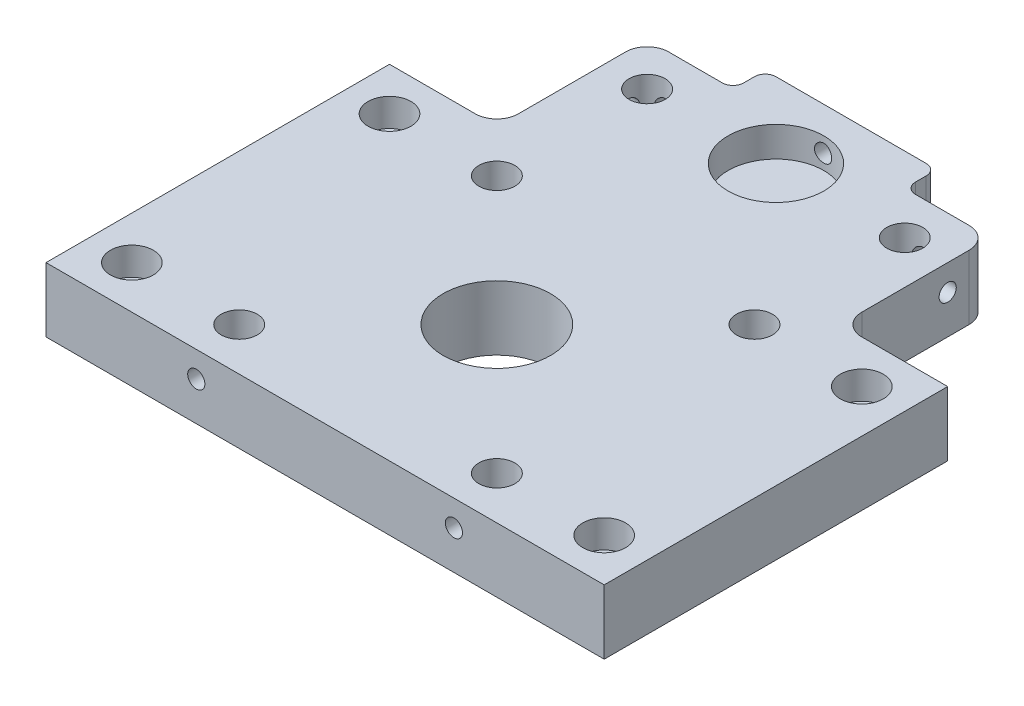
SolidWorks part; units mm, degrees
material "ABS"
ref_plane "Plano frontal" through (0, 0, 0) normal (0, 0, 1) x (1, 0, 0)
ref_plane "Plano superior" through (0, 0, 0) normal (0, 1, 0) x (1, 0, 0)
ref_plane "Plano direito" through (0, 0, 0) normal (1, 0, 0) x (0, 0, -1)
sketch "Esboço1" plane through (0, 0, 0) normal (0, 1, 0) x (1, 0, 0)
  line L1 (65, -65) -> (-65, -65)
  line L2 (65, -65) -> (65, 65)
  line L3 (65, 65) -> (-65, 65)
  line L4 (-65, -65) -> (-65, 65)
  line L5 (65, -65) -> (-65, 65) construction
  line L6 (65, 65) -> (-65, -65) construction
  point P0 (0, 0)
  dimension "D1" = 130
  dimension "D2" = 130
extrude "Ressalto-extrusão1" add sketch "Esboço1" along normal blind 15
sketch "Esboço2" plane through (0, 15, 0) normal (0, 1, 0) x (1, 0, 0)
  line L0 (0, -72.4873) -> (0, 76.1731) construction
  line L1 (-65, 15) -> (65, 15) construction
  line L2 (-65, 65) -> (-65, -65) construction
  line L3 (65, -65) -> (65, 65) construction
  line L4 (-65, -65) -> (65, -65) construction
  line L5 (-40, 65) -> (-40, -65) construction
  line L6 (65, 65) -> (-65, 65) construction
  line L7 (40, 65) -> (40, -65) construction
  line L8 (-65, -25) -> (65, -25) construction
  line L9 (-40, 40) -> (40, 40) construction
  circle A0 centre (-30, 5) radius 4.2
  circle A1 centre (30, 5) radius 4.2
  circle A2 centre (30, -55) radius 4.2
  circle A3 centre (-30, -55) radius 4.2
  circle A4 centre (-30, 40) radius 4.2
  circle A5 centre (30, 40) radius 4.2
  dimension "D5" = 8.4
  dimension "D7" = 10
  dimension "D1" = 80
  dimension "D2" = 40
  dimension "D3" = 40
  dimension "D4" = 40
  dimension "D6" = 10
  dimension "D8" = 25
  dimension "D9" = 10
extrude "Corte-extrusão1" cut sketch "Esboço2" against normal blind 12
sketch "Esboço3" plane through (0, 15, 0) normal (0, 1, 0) x (1, 0, 0)
  line L0 (0, -72.7603) -> (0, 80.4323) construction
  line L1 (-65, 15) -> (65, 15) construction
  line L2 (-65, 65) -> (-65, -65) construction
  line L3 (65, -65) -> (65, 65) construction
  line L4 (-65, -65) -> (65, -65) construction
  line L5 (-65, -25) -> (65, -25) construction
  circle A0 centre (0, -25) radius 12.5
  dimension "D3" = 25
  dimension "D1" = 80
  dimension "D2" = 40
extrude "Corte-extrusão2" cut sketch "Esboço3" against normal through all
sketch "Esboço4" plane through (0, 15, 0) normal (0, 1, 0) x (1, 0, 0)
  line L0 (-65, 15) -> (65, 15) construction
  line L1 (-65, 65) -> (-65, -65) construction
  line L2 (65, -65) -> (65, 65) construction
  line L3 (65, 65) -> (-65, 65) construction
  line L4 (0, 91.3368) -> (0, -92.976) construction
  line L5 (-65, 40) -> (65, 40) construction
  circle A0 centre (0, 40) radius 11.15
  dimension "D3" = 22.3
  dimension "D1" = 50
  dimension "D2" = 25
extrude "Corte-extrusão3" cut sketch "Esboço4" against normal blind 7
sketch "Esboço5" plane through (0, 15, 0) normal (0, 1, 0) x (1, 0, 0)
  line L0 (0, 76.468) -> (0, -74.8954) construction
  line L1 (-65, 65) -> (-40, 65)
  line L2 (-65, 65) -> (-65, 15)
  line L3 (-65, 15) -> (-40, 15)
  line L4 (-40, 65) -> (-40, 15)
  line L5 (40, 65) -> (40, 15)
  line L6 (65, 15) -> (40, 15)
  line L7 (65, 65) -> (65, 15)
  line L8 (65, 65) -> (40, 65)
  dimension "D1" = 50
  dimension "D2" = 25
extrude "Corte-extrusão4" cut sketch "Esboço5" against normal through all
fillet "Filete1" radius 5 2 edges at (40, 7.5, -65) (-40, 7.5, -65)
sketch "Esboço6" plane through (0, 15, 0) normal (0, 1, 0) x (1, 0, 0)
  line L0 (-74.262, -25) -> (70.9857, -25) construction
  line L1 (0, 74.1091) -> (0, -76.8611) construction
  line L2 (-65, 15) -> (-40, 15) construction
  line L3 (-65, 15) -> (-65, -65) construction
  circle A0 centre (-55, 5) radius 5
  circle A1 centre (55, 5) radius 5
  circle A2 centre (55, -55) radius 5
  circle A3 centre (-55, -55) radius 5
  dimension "D1" = 10
  dimension "D3" = 10
  dimension "D2" = 10
extrude "Corte-extrusão5" cut sketch "Esboço6" against normal blind 6.5
sketch "Esboço7" plane through (0, 8.5, 0) normal (0, 1, 0) x (1, 0, 0)
  line L0 (-65, -25) -> (65, -25) construction
  line L1 (-65, 15) -> (-65, -65) construction
  line L2 (65, -65) -> (65, 15) construction
  line L3 (0, 65) -> (0, -65) construction
  line L4 (35, 65) -> (-35, 65) construction
  line L5 (-65, -65) -> (65, -65) construction
  circle A0 centre (-55, 5) radius 3
  circle A1 centre (-55, 5) radius 5 construction
  circle A2 centre (55, 5) radius 3
  circle A3 centre (55, -55) radius 3
  circle A4 centre (-55, -55) radius 3
  dimension "D1" = 6
extrude "Corte-extrusão6" cut sketch "Esboço7" against normal through all
sketch "Esboço8" plane through (0, 15, 0) normal (0, 1, 0) x (1, 0, 0)
  line L0 (0, 95.8386) -> (0, -83.9991) construction
  line L1 (35, 65) -> (-35, 65) construction
  line L2 (7.5, 72.5) -> (-7.5, 72.5)
  line L3 (7.5, 72.5) -> (7.5, 57.5)
  line L4 (7.5, 57.5) -> (-7.5, 57.5)
  line L5 (-7.5, 72.5) -> (-7.5, 57.5)
  line L6 (7.5, 72.5) -> (-7.5, 57.5) construction
  line L7 (7.5, 57.5) -> (-7.5, 72.5) construction
  point P3 (0, 65)
  dimension "D1" = 15
  dimension "D2" = 15
extrude "Corte-extrusão7" cut sketch "Esboço8" against normal through all
sketch "Esboço9" plane through (0, 0, -57.5) normal (0, 0, -1) x (-1, 0, 0)
  line L0 (0, -8.9377) -> (0, 25.8913) construction
  line L1 (7.5, 15) -> (-7.5, 15) construction
  circle A0 centre (0, 11.5) radius 2
  dimension "D1" = 3.5
  dimension "D2" = 4
extrude "Corte-extrusão8" cut sketch "Esboço9" against normal blind 10
sketch "Esboço10" plane through (-40, 0, 0) normal (-1, 0, 0) x (0, 0, 1)
  line L0 (-15, 15) -> (-60, 15) construction
  line L1 (-65, 0) -> (-65, 15) construction
  circle A0 centre (-40, 9) radius 2
  dimension "D1" = 4
  dimension "D2" = 6
  dimension "D3" = 25
extrude "Corte-extrusão9" cut sketch "Esboço10" against normal blind 10
sketch "Esboço11" plane through (40, 0, 0) normal (1, 0, 0) x (0, 0, -1)
  line L0 (65, 15) -> (65, 0) construction
  line L1 (60, 15) -> (15, 15) construction
  circle A0 centre (40, 9) radius 2
  dimension "D1" = 4
  dimension "D2" = 25
  dimension "D3" = 6
extrude "Corte-extrusão10" cut sketch "Esboço11" against normal blind 10
sketch "Esboço12" plane through (0, 0, 65) normal (0, 0, 1) x (1, 0, 0)
  line L0 (-65, 15) -> (-65, 0) construction
  line L1 (-65, 15) -> (65, 15) construction
  line L2 (0, -19.0544) -> (0, 30.5861) construction
  circle A0 centre (-30, 9) radius 2
  circle A1 centre (30, 9) radius 2
  dimension "D1" = 35
  dimension "D2" = 4
  dimension "D3" = 6
extrude "Corte-extrusão11" cut sketch "Esboço12" against normal blind 10
fillet "Filete2" radius 5 2 edges at (-40, 7.5, -15) (40, 7.5, -15)
sketch "Esboço13" plane through (0, 15, 0) normal (0, 1, 0) x (1, 0, 0)
  line L5 (-7.5, 57.5) -> (-20, 57.5)
  line L6 (-40, 20) -> (-40, 60) construction
  line L8 (-30, 34.8368) -> (-30, 45.3155) construction
  line L9 (0, -77.4538) -> (0, 84.4836) construction
  line L14 (-7.5, 57.5) -> (-7.5, 65)
  line L15 (-7.5, 65) -> (-40, 65)
  line L16 (-40, 65) -> (-40, 57.5)
  line L17 (-40, 50) -> (-20, 50)
  line L18 (-20, 50) -> (-20, 57.5)
  line L19 (-40, 50) -> (-40, 57.5)
  line L20 (7.5, 57.5) -> (7.5, 65)
  line L21 (7.5, 65) -> (40, 65)
  line L22 (40, 65) -> (40, 57.5)
  line L23 (40, 50) -> (40, 57.5)
  line L24 (40, 50) -> (20, 50)
  line L25 (20, 50) -> (20, 57.5)
  line L26 (7.5, 57.5) -> (20, 57.5)
  circle A1 centre (-30, 40) radius 4.2 construction
  dimension "D2" = 10
  dimension "D1" = 20
extrude "Corte-extrusão12" cut sketch "Esboço13" against normal through all
sketch "Esboço14" plane through (0, 0, -50) normal (0, 0, -1) x (-1, 0, 0)
  line L0 (-20, 15) -> (-40, 15) construction
  line L1 (-40, 0) -> (-40, 15) construction
  line L2 (0, -18.116) -> (0, 36.5784) construction
  circle A0 centre (-30, 9) radius 2
  circle A1 centre (30, 9) radius 2
  dimension "D1" = 4
  dimension "D2" = 6
  dimension "D3" = 10
extrude "Corte-extrusão13" cut sketch "Esboço14" against normal blind 10
fillet "Filete4" radius 5 2 edges at (-40, 7.5, -50) (40, 7.5, -50)
fillet "Filete5" radius 2.5 4 edges at (-20, 7.5, -50) (-20, 7.5, -57.5) (20, 7.5, -57.5) (20, 7.5, -50)
